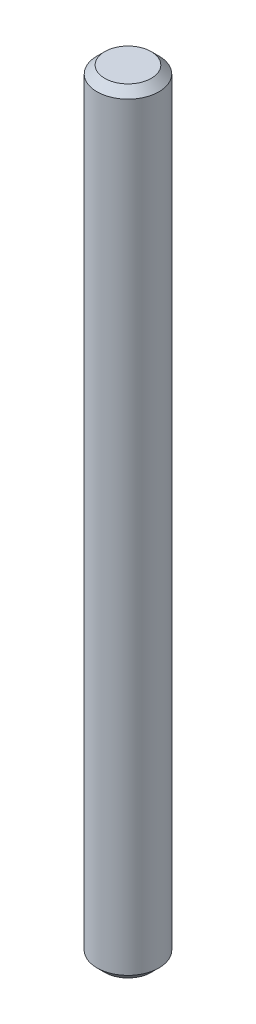
SolidWorks part; units mm, degrees
ref_plane "Front Plane" through (0, 0, 0) normal (0, 0, 1) x (1, 0, 0)
ref_plane "Top Plane" through (0, 0, 0) normal (0, 1, 0) x (1, 0, 0)
ref_plane "Right Plane" through (0, 0, 0) normal (1, 0, 0) x (0, 0, -1)
sketch "Sketch1" plane through (0, 0, 0) normal (0, 1, 0) x (1, 0, 0)
  circle A0 centre (0, 0) radius 4
  dimension "D1" = 8
extrude "Boss-Extrude1" add sketch "Sketch1" along normal blind 100 contours A0
chamfer "Chamfer1" distance 1 angle 45 2 edges at (0, 0, 4) (0, 100, 4)
